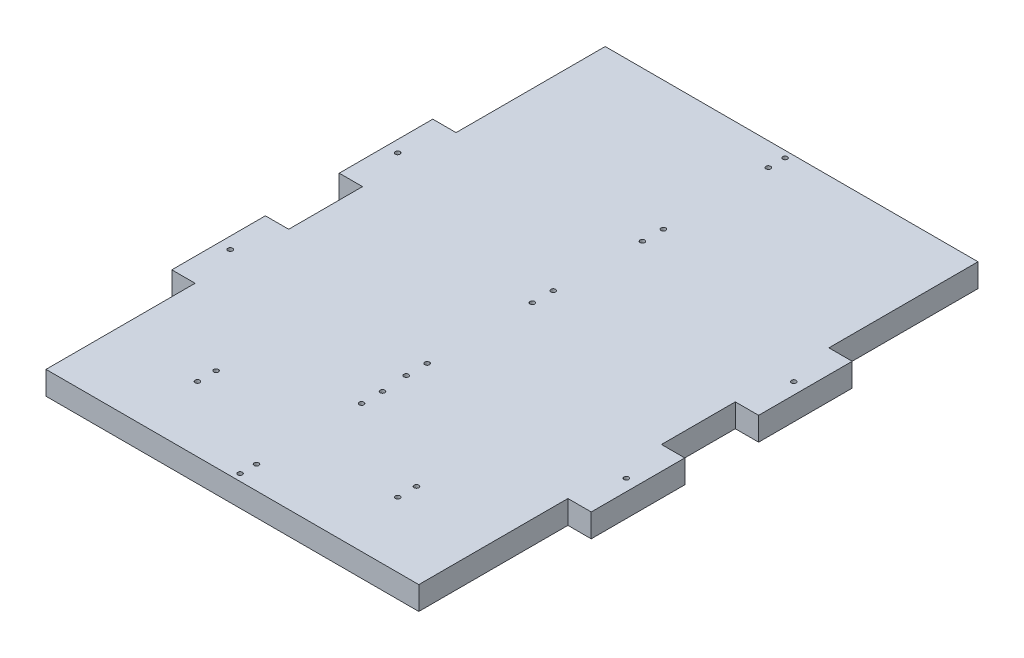
SolidWorks part; units mm, degrees
ref_plane "Front Plane" through (0, 0, 0) normal (0, 0, 1) x (1, 0, 0)
ref_plane "Top Plane" through (0, 0, 0) normal (0, 1, 0) x (1, 0, 0)
ref_plane "Right Plane" through (0, 0, 0) normal (1, 0, 0) x (0, 0, -1)
sketch "Sketch1" plane through (0, 0, 0) normal (0, 1, 0) x (1, 0, 0)
  line L1 (0, 0) -> (101.6, 0)
  line L2 (0, 0) -> (0, 152.4)
  line L3 (0, 152.4) -> (101.6, 152.4)
  line L4 (101.6, 0) -> (101.6, 152.4)
  dimension "D1" = 101.6
  dimension "D2" = 152.4
extrude "Boss-Extrude1" add sketch "Sketch1" along normal blind 6.35
sketch "Sketch2" plane through (101.6, 0, 0) normal (1, 0, 0) x (0, 0, -1)
  line L1 (66.1383, 0) -> (40.64, 0)
  line L2 (66.1383, 0) -> (66.1383, 6.35)
  line L3 (66.1383, 6.35) -> (40.64, 6.35)
  line L4 (40.64, 0) -> (40.64, 6.35)
  line L5 (86.2617, 0) -> (111.76, 0)
  line L6 (86.2617, 0) -> (86.2617, 6.35)
  line L7 (86.2617, 6.35) -> (111.76, 6.35)
  line L8 (111.76, 0) -> (111.76, 6.35)
extrude "Boss-Extrude2" add sketch "Sketch2" along normal blind 6.35
sketch "Sketch3" plane through (0, 0, 0) normal (-1, 0, 0) x (0, 0, 1)
  line L1 (-86.2617, 0) -> (-111.76, 0)
  line L2 (-86.2617, 0) -> (-86.2617, 6.35)
  line L3 (-86.2617, 6.35) -> (-111.76, 6.35)
  line L4 (-111.76, 0) -> (-111.76, 6.35)
  line L5 (-66.1383, 0) -> (-40.64, 0)
  line L6 (-66.1383, 0) -> (-66.1383, 6.35)
  line L7 (-66.1383, 6.35) -> (-40.64, 6.35)
  line L8 (-40.64, 0) -> (-40.64, 6.35)
extrude "Boss-Extrude3" add sketch "Sketch3" along normal blind 6.35
sketch "Sketch4" plane through (0, 0, 0) normal (0, -1, 0) x (1, 0, 0)
  line L0 (-3.175, -40.64) -> (-3.175, -53.3891) construction
  line L1 (0, -40.64) -> (-6.35, -40.64) construction
  line L2 (0, -40.64) -> (0, -66.1383) construction
  line L3 (0, -66.1383) -> (-6.35, -66.1383) construction
  line L4 (-6.35, -40.64) -> (-6.35, -66.1383) construction
  line L5 (0, -86.2617) -> (-6.35, -86.2617) construction
  line L6 (0, -86.2617) -> (0, -111.76) construction
  line L7 (0, -111.76) -> (-6.35, -111.76) construction
  line L8 (-6.35, -86.2617) -> (-6.35, -111.76) construction
  line L9 (101.6, -86.2617) -> (107.95, -86.2617) construction
  line L10 (101.6, -86.2617) -> (101.6, -111.76) construction
  line L11 (101.6, -111.76) -> (107.95, -111.76) construction
  line L12 (107.95, -86.2617) -> (107.95, -111.76) construction
  line L13 (101.6, -66.1383) -> (107.95, -66.1383) construction
  line L14 (101.6, -66.1383) -> (101.6, -40.64) construction
  line L15 (101.6, -40.64) -> (107.95, -40.64) construction
  line L16 (107.95, -66.1383) -> (107.95, -40.64) construction
  line L17 (-3.175, -53.3891) -> (-6.35, -53.3891) construction
  line L18 (-3.175, -86.2617) -> (-3.175, -99.0109) construction
  line L19 (-3.175, -99.0109) -> (-6.35, -99.0109) construction
  line L20 (-6.35, -99.0109) -> (104.775, -99.0109) construction
  line L21 (104.775, -99.0109) -> (104.775, -86.2617) construction
  line L22 (104.775, -86.2617) -> (104.775, -53.3891) construction
  line L23 (104.775, -53.3891) -> (107.95, -53.3891) construction
  circle A0 centre (-3.175, -53.3891) radius 0.635
  circle A1 centre (-3.175, -99.0109) radius 0.635
  circle A2 centre (104.775, -53.3891) radius 0.635
  circle A3 centre (104.775, -99.0109) radius 0.635
extrude "Cut-Extrude1" cut sketch "Sketch4" against normal blind 6.35
sketch "Sketch5" plane through (0, 0, 0) normal (0, -1, 0) x (1, 0, 0)
  circle A0 centre (51.054, -6.3046) radius 0.635
  circle A1 centre (51.054, -34.9408) radius 0.635
  circle A2 centre (51.054, -40.6558) radius 0.635
  circle A3 centre (51.054, -1.8596) radius 0.635
  circle A4 centre (50.5308, -87.7042) radius 0.635
  circle A5 centre (50.546, -47.629) radius 0.635
  circle A6 centre (50.546, -53.344) radius 0.635
  circle A7 centre (50.5443, -81.9892) radius 0.635
  circle A8 centre (51.054, -111.4983) radius 0.635
  circle A11 centre (51.054, -117.2133) radius 0.635
  point P26 (51.054, -40.6558)
  point P27 (51.054, -34.9408)
  point P31 (51.054, -1.8596)
  point P33 (51.054, -6.3046)
  point P34 (51.054, -1.8596)
  dimension "D1" = 4.445
  dimension "D2" = 1.27
  dimension "D3" = 5.715
  dimension "D4" = 5.715
  dimension "D5" = 5.715
  dimension "D6" = 5.715
extrude "Cut-Extrude2" cut sketch "Sketch5" against normal through all
sketch "Sketch7" plane through (0, 6.35, 0) normal (0, 1, 0) x (1, 0, 0)
  line L0 (23.495, 17.78) -> (23.495, 0) construction
  line L1 (0, 0) -> (101.6, 0) construction
  line L2 (23.495, 17.78) -> (0, 17.78) construction
  line L3 (0, 40.64) -> (0, 0) construction
  line L4 (23.495, 22.86) -> (0, 22.86) construction
  line L5 (23.495, 22.86) -> (23.495, 17.78) construction
  line L6 (78.105, 17.78) -> (78.105, 0) construction
  line L7 (78.105, 22.86) -> (78.105, 17.78) construction
  line L8 (78.105, 22.86) -> (101.6, 22.86) construction
  line L9 (101.6, 0) -> (101.6, 40.64) construction
  line L10 (78.105, 17.78) -> (101.6, 17.78) construction
  circle A0 centre (23.495, 17.78) radius 0.635
  circle A1 centre (23.495, 22.86) radius 0.635
  circle A2 centre (78.105, 22.86) radius 0.635
  circle A3 centre (78.105, 17.78) radius 0.635
  dimension "D1" = 1.27
  dimension "D2" = 23.495
  dimension "D3" = 5.08
  dimension "D4" = 17.78
extrude "Cut-Extrude3" cut sketch "Sketch7" against normal through all
sketch "Sketch8" plane through (0, 0, 0) normal (0, -1, 0) x (1, 0, 0)
sketch "Sketch9" plane through (0, 6.35, 0) normal (0, 1, 0) x (1, 0, 0)
  line L0 (50.8, 150.622) -> (50.8, 152.4) construction
  line L1 (101.6, 152.4) -> (0, 152.4) construction
  line L2 (50.8, 146.05) -> (50.8, 150.622) construction
  line L3 (0, 152.4) -> (0, 111.76) construction
  line L4 (50.8, 150.622) -> (0, 150.622) construction
  circle A0 centre (50.8, 150.622) radius 0.635
  circle A1 centre (50.8, 146.05) radius 0.635
  dimension "D1" = 1.27
  dimension "D2" = 4.572
  dimension "D3" = 1.778
  dimension "D4" = 50.8
extrude "Cut-Extrude4" cut sketch "Sketch9" against normal through all
